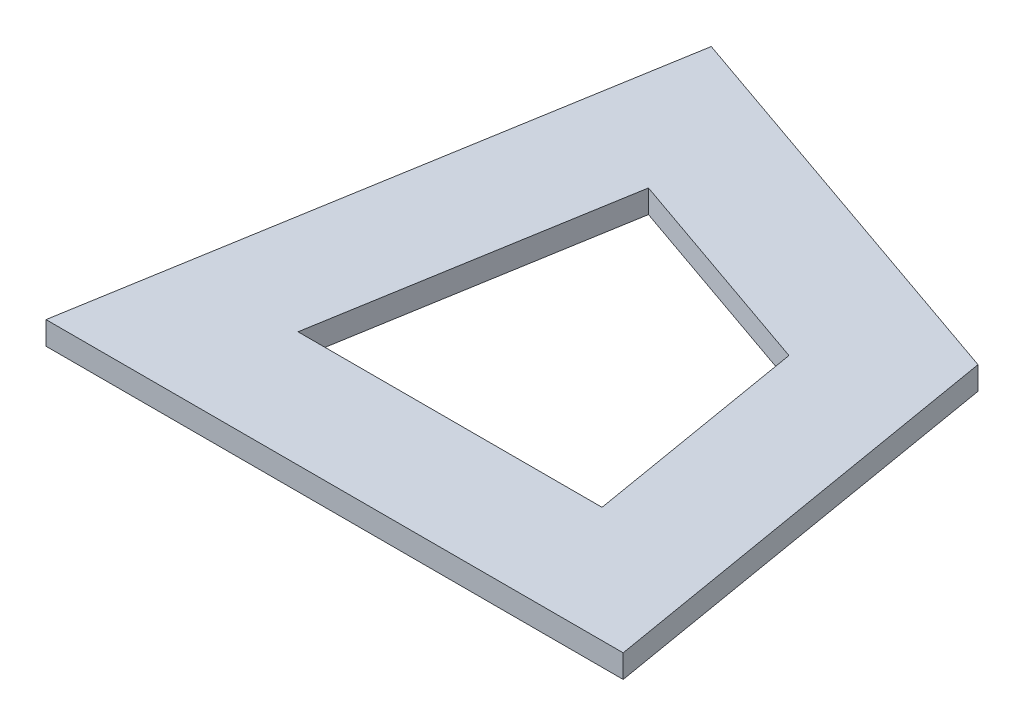
SolidWorks part; units mm, degrees
ref_plane "Front Plane" through (0, 0, 0) normal (0, 0, 1) x (1, 0, 0)
ref_plane "Top Plane" through (0, 0, 0) normal (0, 1, 0) x (1, 0, 0)
ref_plane "Right Plane" through (0, 0, 0) normal (1, 0, 0) x (0, 0, -1)
sketch "Sketch1" plane through (0, 0, 0) normal (0, 1, 0) x (1, 0, 0)
  line L0 (0, 0) -> (50, 0)
  line L1 (50, 0) -> (43.7506, 36.9879)
  line L2 (43.7506, 36.9879) -> (8.3298, 49.3013)
  line L3 (8.3298, 49.3013) -> (0, 0)
  line L4 (16.2194, 35.9716) -> (11.8313, 10)
  line L5 (11.8313, 10) -> (38.1687, 10)
  line L6 (38.1687, 10) -> (34.8764, 29.4858)
  line L7 (34.8764, 29.4858) -> (16.2194, 35.9716)
  dimension "D1" = 50
  dimension "D2" = 37.5
  dimension "D3" = 80.41
  dimension "D4" = 80.41
  dimension "D6" = 80.421
  dimension "D5" = 10
extrude "Boss-Extrude1" add sketch "Sketch1" along normal blind 2
